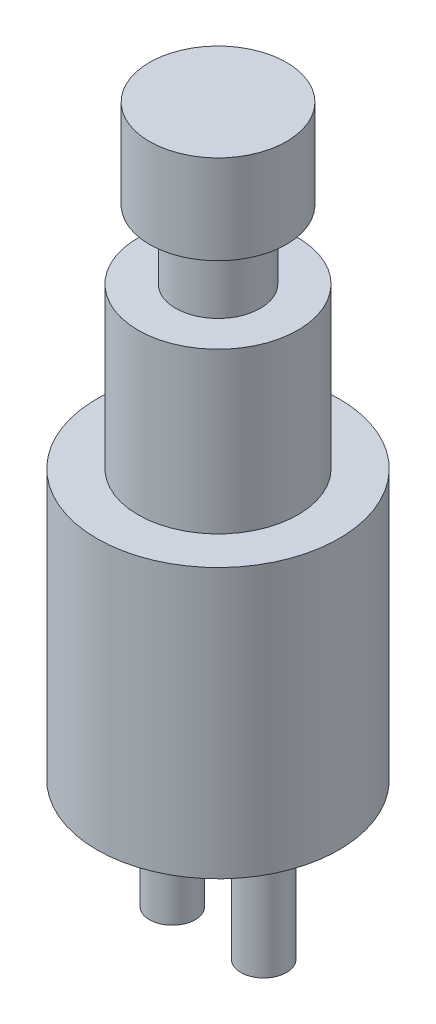
SolidWorks part; units mm, degrees
ref_plane "Front Plane" through (0, 0, 0) normal (0, 0, 1) x (1, 0, 0)
ref_plane "Top Plane" through (0, 0, 0) normal (0, 1, 0) x (1, 0, 0)
ref_plane "Right Plane" through (0, 0, 0) normal (1, 0, 0) x (0, 0, -1)
sketch "Sketch2" plane through (0, 0, 0) normal (0, 1, 0) x (1, 0, 0)
  circle A0 centre (0, 0) radius 5.3
extrude "Boss-Extrude1" add sketch "Sketch2" along normal blind 11.8
sketch "Sketch3" plane through (0, 11.8, 0) normal (0, 1, 0) x (1, 0, 0)
  circle A0 centre (0, 0) radius 3.5
extrude "Boss-Extrude2" add sketch "Sketch3" along normal blind 7
sketch "Sketch4" plane through (0, 18.8, 0) normal (0, 1, 0) x (1, 0, 0)
  circle A0 centre (0, 0) radius 1.85
extrude "Boss-Extrude3" add sketch "Sketch4" along normal blind 3
sketch "Sketch5" plane through (0, 21.8, 0) normal (0, 1, 0) x (1, 0, 0)
  circle A0 centre (0, 0) radius 3
extrude "Boss-Extrude4" add sketch "Sketch5" along normal blind 3.9
sketch "Sketch6" plane through (0, 0, 0) normal (0, -1, 0) x (-1, 0, 0)
  circle A0 centre (2, 0) radius 1
  circle A1 centre (-2, 0) radius 1
  dimension "D1" = 4
  dimension "D2" = 2
extrude "Boss-Extrude5" add sketch "Sketch6" along normal blind 5.8
